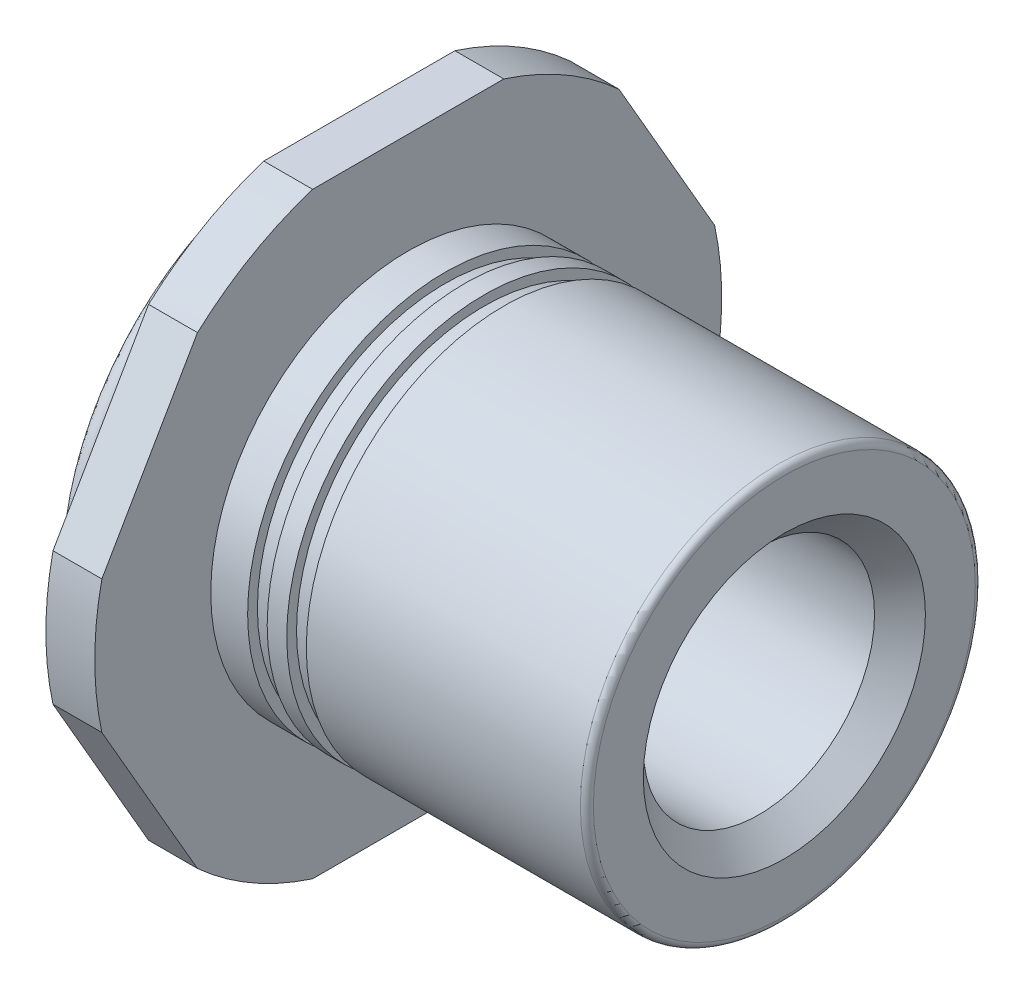
SolidWorks part; units mm, degrees
ref_plane "Front Plane" through (0, 0, 0) normal (0, 0, 1) x (1, 0, 0)
ref_plane "Top Plane" through (0, 0, 0) normal (0, 1, 0) x (1, 0, 0)
ref_plane "Right Plane" through (0, 0, 0) normal (1, 0, 0) x (0, 0, -1)
ref_plane "Plane4" through (-0.52, 0, 0) normal (-1, 0, 0) x (0, -1, 0)
sketch "Sketch1" plane through (-0.52, 0, 0) normal (-1, 0, 0) x (0, -1, 0)
  line L0 (-3.175, 1.0165) -> (-3.175, -1.0165)
  line L1 (-2.4678, -2.2414) -> (-0.7072, -3.2579)
  line L2 (0.7072, -3.2579) -> (2.4678, -2.2414)
  line L3 (3.175, -1.0165) -> (3.175, 1.0165)
  line L4 (2.4678, 2.2414) -> (0.7072, 3.2579)
  line L5 (-0.7072, 3.2579) -> (-2.4678, 2.2414)
  arc A0 (-3.175, -1.0165) -> (-2.4678, -2.2414) centre (0, 0) ccw
  arc A1 (-0.7072, -3.2579) -> (0.7072, -3.2579) centre (0, 0) ccw
  arc A2 (2.4678, -2.2414) -> (3.175, -1.0165) centre (0, 0) ccw
  arc A3 (3.175, 1.0165) -> (2.4678, 2.2414) centre (0, 0) ccw
  arc A4 (0.7072, 3.2579) -> (-0.7072, 3.2579) centre (0, 0) ccw
  arc A5 (-2.4678, 2.2414) -> (-3.175, 1.0165) centre (0, 0) ccw
extrude "Boss-Extrude1" add sketch "Sketch1" against normal blind 0.52
ref_plane "Plane5" through (0, 0, 0) normal (0, 0, -1) x (-1, 0, 0)
sketch "Sketch2" plane through (0, 0, 0) normal (0, 0, -1) x (-1, 0, 0)
  line L0 (0.52, 2.4954) -> (0.52, 0)
  line L1 (0.52, 0) -> (1.04, 0)
  line L2 (1.04, 0) -> (1.04, 2.591)
  line L3 (0.8625, 2.6645) -> (0.6933, 2.4954)
  line L4 (0.6933, 2.4954) -> (0.52, 2.4954)
  line L5 (0.52, 0) -> (1.0459, 0) construction
  spline S0 degree 3 poles (0.8625, 2.6645) (0.8707, 2.6728) (0.8805, 2.6797) (0.8909, 2.6847) (0.9014, 2.6898) (0.9129, 2.6931) (0.9245, 2.6944) (0.9361, 2.6956) (0.948, 2.695) (0.9594, 2.6923) (0.9707, 2.6897) (0.9818, 2.6851) (0.9916, 2.6789) (1.0014, 2.6727) (1.0103, 2.6647) (1.0176, 2.6555) (1.0248, 2.6464) (1.0305, 2.6359) (1.0343, 2.6249) (1.0381, 2.6141) (1.04, 2.6025) (1.04, 2.591) knots 0 0 0 0 0.000035 0.000035 0.000035 0.00007 0.00007 0.00007 0.000105 0.000105 0.000105 0.00014 0.00014 0.00014 0.000175 0.000175 0.000175 0.00021 0.00021 0.00021 0.000244 0.000244 0.000244 0.000244
revolve "Revolve1" add sketch "Sketch2" angle 360 about L5
sketch "Sketch3" plane through (0, 0, 0) normal (0, 0, -1) x (-1, 0, 0)
  line L0 (-4, 2.1) -> (-4, 0)
  line L1 (-4, 0) -> (0, 0)
  line L2 (0, 0) -> (0, 2.1)
  line L3 (0, 2.1) -> (-0.392, 2.1)
  line L4 (-0.392, 2.1) -> (-0.392, 1.996)
  line L5 (-0.392, 1.996) -> (-0.6, 1.996)
  line L6 (-0.6, 1.996) -> (-0.6, 2.1)
  line L7 (-0.6, 2.1) -> (-0.808, 2.1)
  line L8 (-0.808, 2.1) -> (-0.808, 1.996)
  line L9 (-0.808, 1.996) -> (-1.016, 1.996)
  line L10 (-1.016, 1.996) -> (-1.016, 2.1)
  line L11 (-1.016, 2.1) -> (-4, 2.1)
  line L12 (-4, 0) -> (0, 0) construction
revolve "Revolve2" add sketch "Sketch3" angle 360 about L12
hole_wizard "M2 Clearance Hole1" positions "Sketch5" profile "Sketch4" hole size "M2" standard "ANSI Metric"
sketch "Sketch5" plane through (-1.04, 0, 0) normal (-1, 0, 0) x (0, 0, 1)
  point P0 (0, 0)
sketch "Sketch4" plane through (-1.04, 0, 0) normal (0, 1, 0) x (0, 0, 1)
  line L0 (0, 0) -> (0, 5.04)
  line L1 (0, 5.04) -> (1.2295, 5.04)
  line L2 (1.2295, 5.04) -> (1.2295, 0)
  line L5 (1.2295, 0) -> (0, 0)
  line L11 (0, -6.35) -> (0, 107.95) construction
  dimension "Thru Hole Dia." = 2.459
  dimension "Thru Hole Depth" = 5.04
chamfer "Chamfer1" distance 0.2705 angle 45 2 edges at (4, 0, 1.2295) (-1.04, 0, 1.2295)
fillet "Fillet1" radius 0.0693 1 edges at (4, 0, 2.1)
